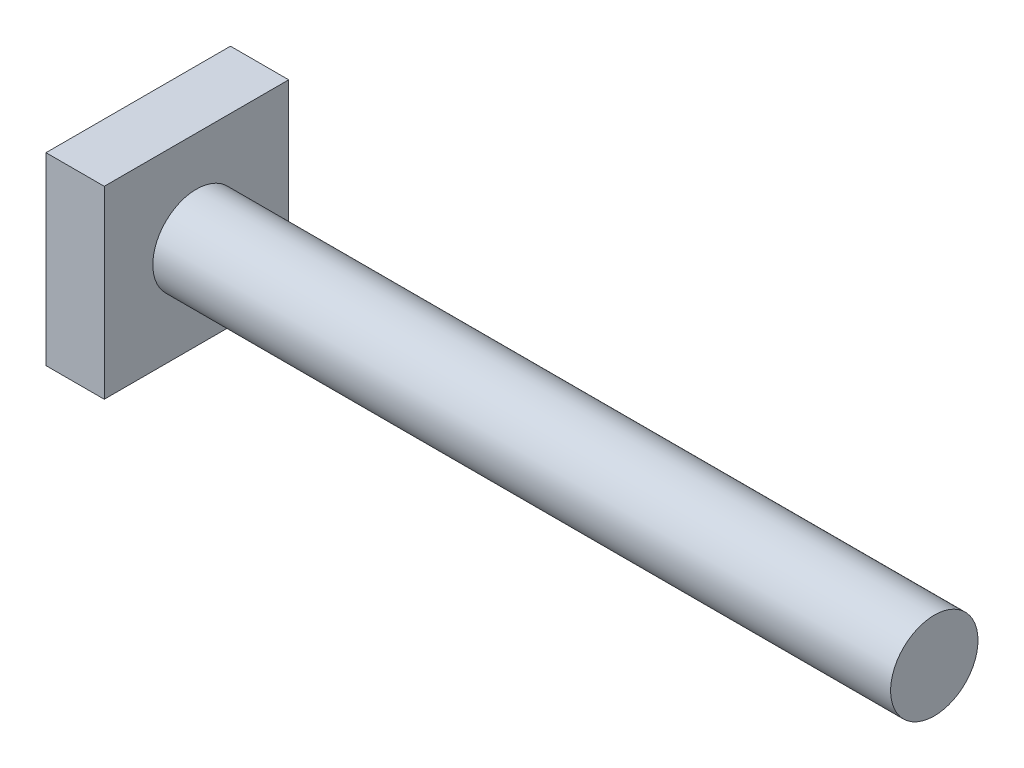
SolidWorks part; units mm, degrees
ref_plane "Front Plane" through (0, 0, 0) normal (0, 0, 1) x (1, 0, 0)
ref_plane "Top Plane" through (0, 0, 0) normal (0, 1, 0) x (1, 0, 0)
ref_plane "Right Plane" through (0, 0, 0) normal (1, 0, 0) x (0, 0, -1)
sketch "Sketch1" plane through (0, 0, 0) normal (1, 0, 0) x (0, 0, -1)
  circle A0 centre (0, 0) radius 114.3
  dimension "D1" = 228.6
extrude "Boss-Extrude1" add sketch "Sketch1" along normal blind 1930.4
sketch "Sketch2" plane through (0, 0, 0) normal (-1, 0, 0) x (0, 0, 1)
  line L1 (-241.3, -241.3) -> (241.3, -241.3)
  line L2 (-241.3, -241.3) -> (-241.3, 241.3)
  line L3 (-241.3, 241.3) -> (241.3, 241.3)
  line L4 (241.3, -241.3) -> (241.3, 241.3)
  line L5 (-241.3, -241.3) -> (241.3, 241.3) construction
  line L6 (-241.3, 241.3) -> (241.3, -241.3) construction
  point P0 (0, 0)
  dimension "D1" = 482.6
extrude "Boss-Extrude2" add sketch "Sketch2" along normal blind 152.4
